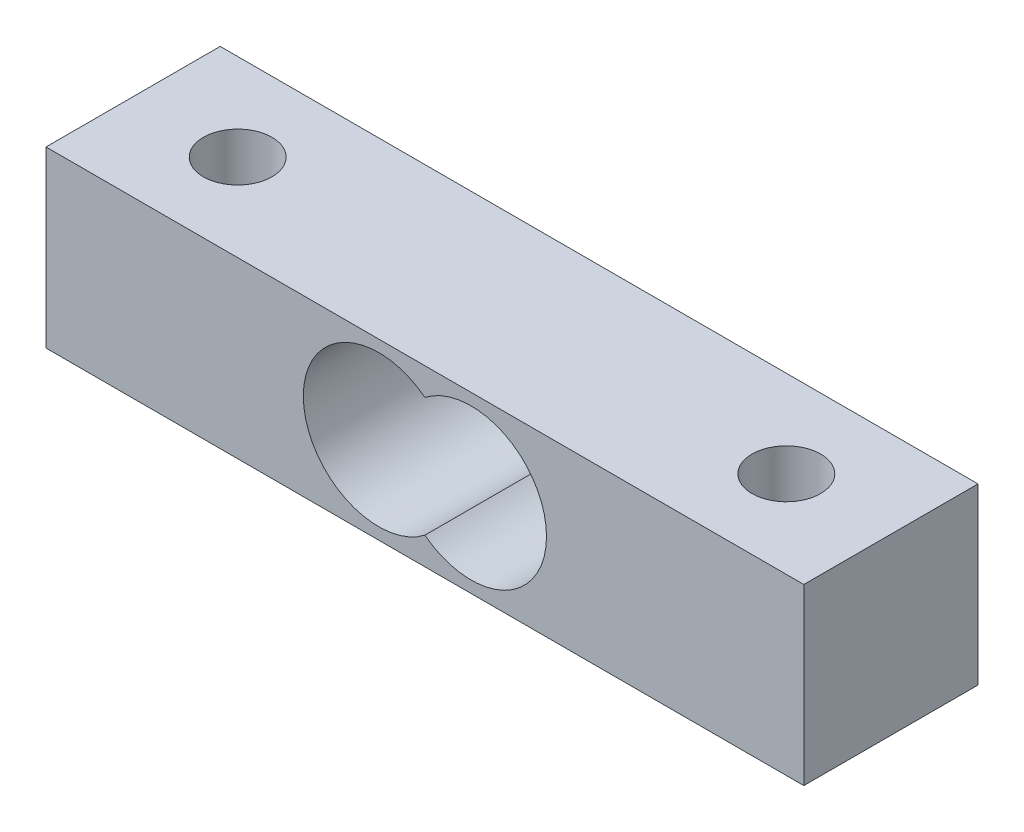
SolidWorks part; units mm, degrees
ref_plane "Plan de face" through (0, 0, 0) normal (0, 0, 1) x (1, 0, 0)
ref_plane "Plan de dessus" through (0, 0, 0) normal (0, 1, 0) x (1, 0, 0)
ref_plane "Plan de droite" through (0, 0, 0) normal (1, 0, 0) x (0, 0, -1)
sketch "Esquisse1" plane through (0, 0, 0) normal (0, 0, 1) x (1, 0, 0)
  line L0 (0, 0) -> (27.625, 0)
  line L1 (0, 0) -> (0, 12.7)
  line L2 (0, 12.7) -> (27.625, 12.7)
  line L3 (0, 6.35) -> (27.625, 6.35) construction
  line L4 (27.625, 12.7) -> (27.625, 0) construction
  line L5 (27.625, 12.7) -> (27.625, 10.7)
  line L6 (27.625, 2) -> (27.625, 0)
  arc A0 (27.625, 10.7) -> (27.625, 2) centre (24.2594, 6.35) ccw
  dimension "D3" = 2
  dimension "D4" = 5.5
  dimension "D1" = 12.7
  dimension "D2" = 27.625
extrude "Boss.-Extru.2" add sketch "Esquisse1" along normal blind 12.7
sketch "Esquisse3" plane through (0, 12.7, 0) normal (0, 1, 0) x (1, 0, 0)
  line L0 (0, -6.35) -> (27.625, -6.35) construction
  line L1 (0, -12.7) -> (0, 0) construction
  line L2 (27.625, -12.7) -> (27.625, 0) construction
  circle A0 centre (7.625, -6.35) radius 2.5
  dimension "D1" = 5
  dimension "D2" = 20
extrude "Enlèv. mat.-Extru.1" cut sketch "Esquisse3" against normal up to next (12.7 mm away)
mirror "Symétrie1" about plane through (27.625, 12.7, 12.7) normal (-1, 0, 0) of "Boss.-Extru.2", "Enlèv. mat.-Extru.1"
